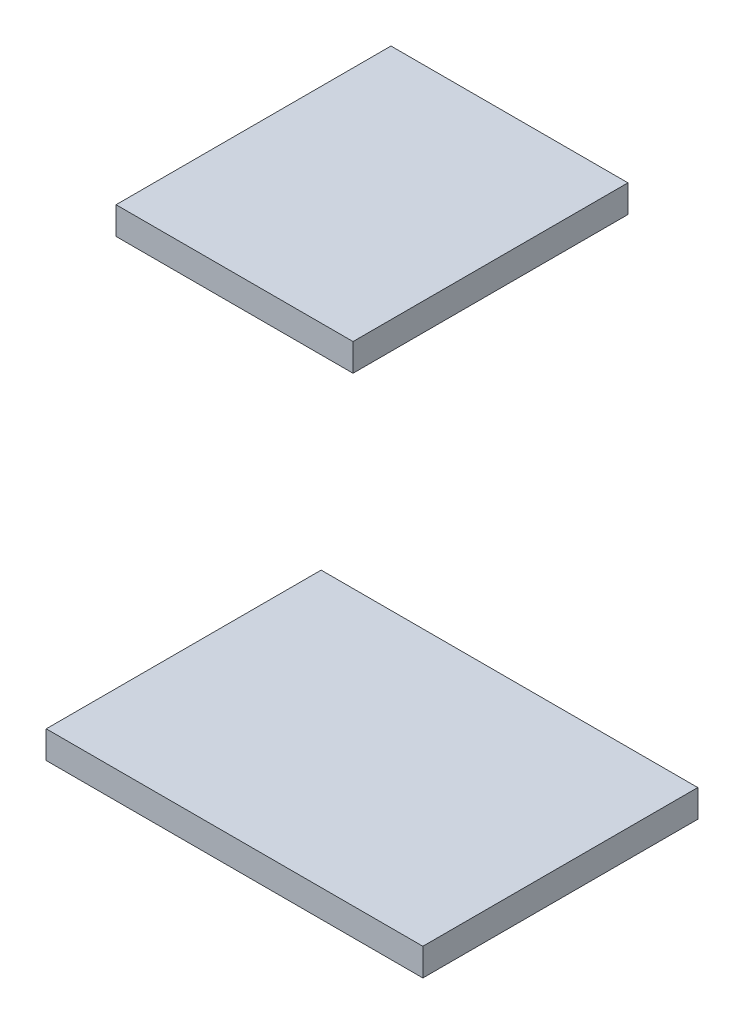
SolidWorks part; units mm, degrees
ref_plane "Ebene vorne" through (0, 0, 0) normal (0, 0, 1) x (1, 0, 0)
ref_plane "Ebene oben" through (0, 0, 0) normal (0, 1, 0) x (1, 0, 0)
ref_plane "Ebene rechts" through (0, 0, 0) normal (1, 0, 0) x (0, 0, -1)
sketch "Skizze1" plane through (0, 0, 0) normal (0, 0, 1) x (1, 0, 0)
  line L1 (133.83, -32.58) -> (142.45, -32.58)
  line L2 (133.83, -32.58) -> (133.83, -33.58)
  line L3 (133.83, -33.58) -> (142.45, -33.58)
  line L4 (142.45, -32.58) -> (142.45, -33.58)
  line L5 (131.29, -50.36) -> (144.99, -50.36)
  line L6 (131.29, -50.36) -> (131.29, -51.36)
  line L7 (131.29, -51.36) -> (144.99, -51.36)
  line L8 (144.99, -50.36) -> (144.99, -51.36)
  circle A0 centre (141.95, -33.08) radius 0.5 construction
  circle A1 centre (134.33, -33.08) radius 0.5 construction
  circle A2 centre (136.87, -33.08) radius 0.5 construction
  circle A3 centre (131.79, -50.86) radius 0.5 construction
  circle A4 centre (134.33, -50.86) radius 0.5 construction
  circle A5 centre (144.49, -50.86) radius 0.5 construction
extrude "Aufsatz-Linear austragen1" add sketch "Skizze1" along normal blind 10
